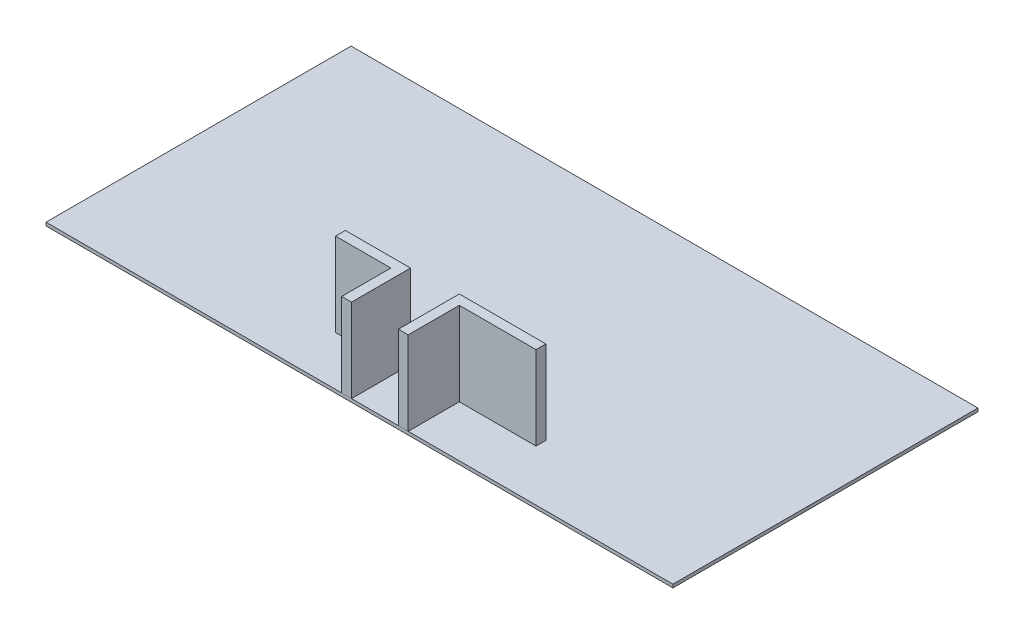
SolidWorks part; units mm, degrees
ref_plane "Front Plane" through (0, 0, 0) normal (0, 0, 1) x (1, 0, 0)
ref_plane "Top Plane" through (0, 0, 0) normal (0, 1, 0) x (1, 0, 0)
ref_plane "Right Plane" through (0, 0, 0) normal (1, 0, 0) x (0, 0, -1)
sketch "Sketch1" plane through (0, 0, 0) normal (0, 1, 0) x (1, 0, 0)
  line L0 (300, 0) -> (-1687.5971, 0)
  line L1 (-1687.5971, 0) -> (-1687.5971, -300)
  line L2 (-1687.5971, -300) -> (0, -300)
  line L3 (0, -300) -> (0, -1800)
  line L4 (0, -1800) -> (300, -1800)
  line L5 (300, -1800) -> (300, 0)
  line L6 (1730, 60) -> (4369.5644, 60)
  line L7 (2030, -1800) -> (2030, -240)
  line L8 (2030, -1800) -> (1730, -1800)
  line L9 (2030, -240) -> (4369.5644, -240)
  line L10 (4369.5644, -240) -> (4369.5644, 60)
  line L11 (1730, -1800) -> (1730, 60)
  dimension "D1" = 1430
  dimension "D2" = 300
  dimension "D3" = 300
  dimension "D4" = 300
  dimension "D5" = 1500
  dimension "D6" = 300
  dimension "D7" = 60
extrude "Boss-Extrude1" add sketch "Sketch1" along normal blind 2550
sketch "Sketch2" plane through (0, 0, 0) normal (0, -1, 0) x (1, 0, 0)
  line L1 (-9023.7436, 1800) -> (10107.5864, 1800)
  line L2 (-9023.7436, 1800) -> (-9023.7436, -7509.6048)
  line L3 (-9023.7436, -7509.6048) -> (10107.5864, -7509.6048)
  line L4 (10107.5864, 1800) -> (10107.5864, -7509.6048)
extrude "Boss-Extrude2" add sketch "Sketch2" along normal blind 100 separate body
